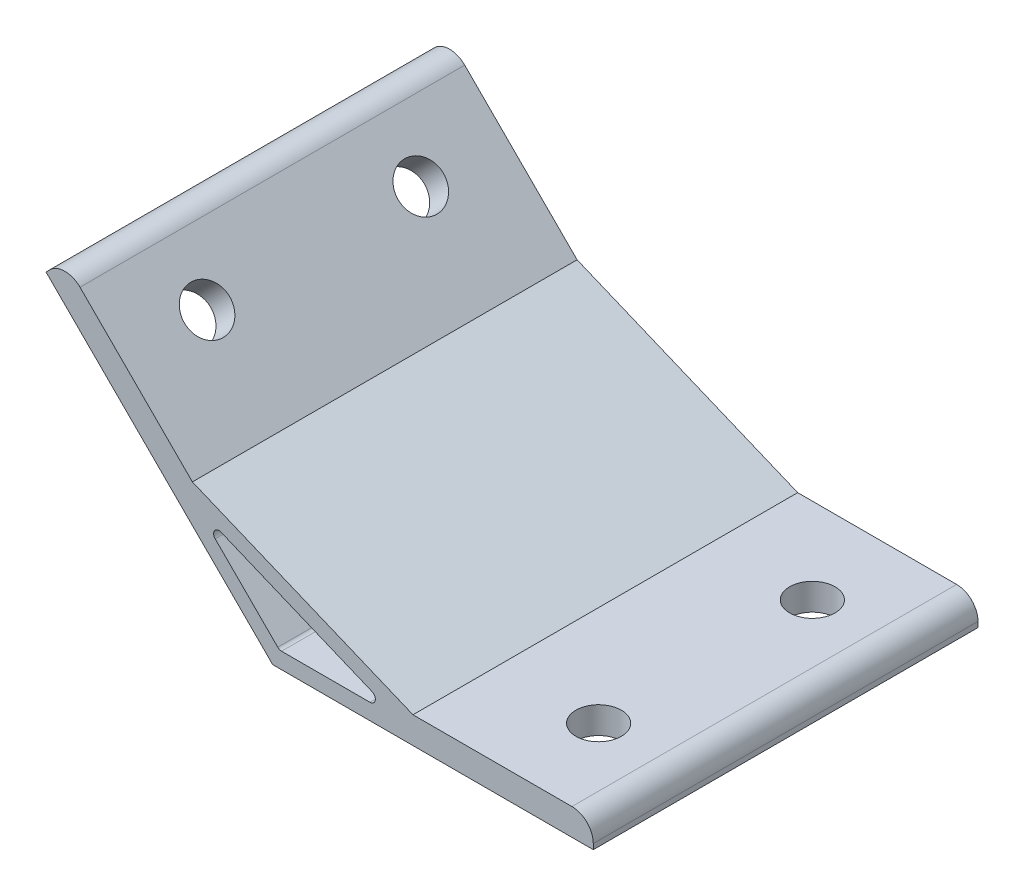
SolidWorks part; units mm, degrees
material "6063 T5"
ref_plane "Спереди" through (0, 0, 0) normal (0, 0, 1) x (1, 0, 0)
ref_plane "Сверху" through (0, 0, 0) normal (0, 1, 0) x (1, 0, 0)
ref_plane "Справа" through (0, 0, 0) normal (1, 0, 0) x (0, 0, -1)
sketch "Эскиз1" plane through (0, 0, 0) normal (0, 0, 1) x (1, 0, 0)
  line L0 (0, 0) -> (-42.4264, 42.4264)
  line L1 (-42.4264, 42.4264) -> (-38.8909, 45.9619)
  line L2 (-38.8909, 45.9619) -> (-15.0286, 22.0996)
  line L3 (-15.0286, 22.0996) -> (26.2536, 5)
  line L4 (26.2536, 5) -> (60, 5)
  line L5 (60, 5) -> (60, 0)
  line L6 (60, 0) -> (0, 0)
  line L7 (-14.3137, 18.5563) -> (23.2426, 3)
  line L8 (23.2426, 3) -> (1.2426, 3)
  line L9 (1.2426, 3) -> (-14.3137, 18.5563)
  line L10 (12.2426, 3) -> (12.2426, 0) construction
  line L11 (-6.5355, 10.7782) -> (-8.6569, 8.6569) construction
  line L12 (0, 0) -> (4.4645, 10.7782) construction
  dimension "D1" = 60
  dimension "D2" = 135
  dimension "D3" = 3
  dimension "D4" = 5
  dimension "D5" = 3
  dimension "D6" = 22
extrude "Бобышка-Вытянуть1" add sketch "Эскиз1" along normal mid plane 72
sketch "Эскиз2" plane through (0, 0, 0) normal (-0.7071, -0.7071, 0) x (0, 0, 1)
  line L0 (36, 60) -> (-36, 60) construction
  line L1 (-20, 45) -> (20, 45) construction
  line L2 (-36, 60) -> (-36, 0) construction
  circle A0 centre (-20, 45) radius 4.25
  circle A1 centre (20, 45) radius 4.25
  point P2 (0, 45)
  dimension "D1" = 8.5
  dimension "D2" = 15
  dimension "D4" = 16
  dimension "D3" = 40
extrude "Вырез-Вытянуть1" cut sketch "Эскиз2" against normal up to surface (5 mm away) up to face at (-26.9597, 34.0308, 0)
sketch "Эскиз3" plane through (0, 0, 0) normal (0, -1, 0) x (1, 0, 0)
  line L0 (60, 36) -> (60, -36) construction
  line L1 (45, 20) -> (45, -20) construction
  circle A0 centre (45, 20) radius 4.25
  circle A1 centre (45, -20) radius 4.25
  point P2 (45, 0)
  dimension "D1" = 8.5
  dimension "D2" = 15
  dimension "D3" = 40
extrude "Вырез-Вытянуть2" cut sketch "Эскиз3" against normal up to surface (5 mm away) up to face at (43.1268, 5, 0)
fillet "Скругление1" radius 4 2 edges at (60, 5, 0) (-38.8909, 45.9619, 0)
fillet "Скругление2" radius 1 3 edges at (-14.3137, 18.5563, 0) (1.2426, 3, 0) (23.2426, 3, 0)
